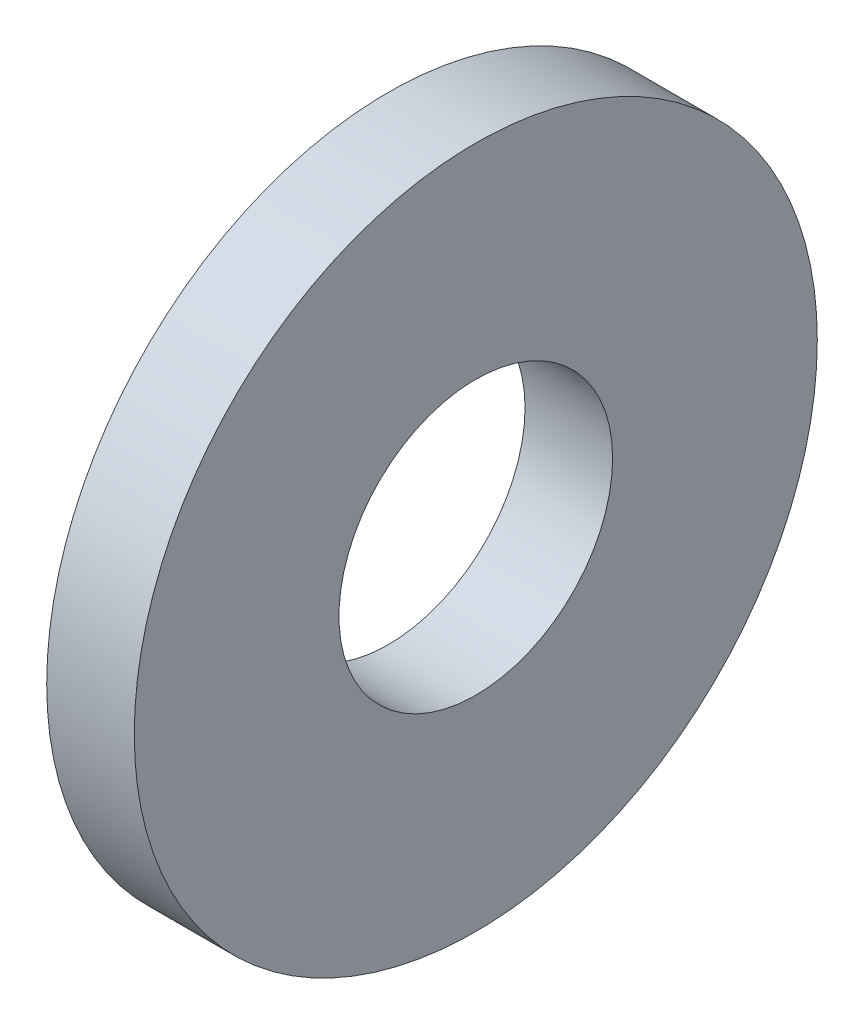
SolidWorks part; units mm, degrees
ref_plane "Front Plane" through (0, 0, 0) normal (0, 0, 1) x (1, 0, 0)
ref_plane "Top Plane" through (0, 0, 0) normal (0, 1, 0) x (1, 0, 0)
ref_plane "Right Plane" through (0, 0, 0) normal (1, 0, 0) x (0, 0, -1)
sketch "Sketch1" plane through (0, 0, 0) normal (1, 0, 0) x (0, 0, -1)
  circle A0 centre (0, 0) radius 3.9624
  circle A1 centre (0, 0) radius 1.5875
  dimension "OD" = 7.9248
  dimension "ID" = 3.175
extrude "Boss-Extrude1" add sketch "Sketch1" along normal blind 1.016
